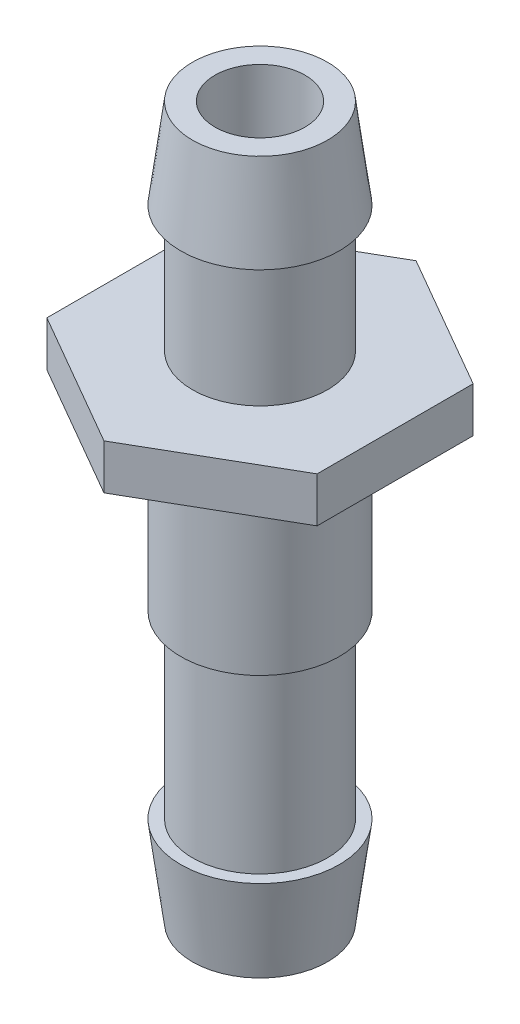
SolidWorks part; units mm, degrees
material "1060 Alloy"
ref_plane "Front Plane" through (0, 0, 0) normal (0, 0, 1) x (1, 0, 0)
ref_plane "Top Plane" through (0, 0, 0) normal (0, 1, 0) x (1, 0, 0)
ref_plane "Right Plane" through (0, 0, 0) normal (1, 0, 0) x (0, 0, -1)
sketch "Sketch1" plane through (0, 0, 0) normal (0, 1, 0) x (1, 0, 0)
  circle A0 centre (0, 0) radius 4.7625
  circle A1 centre (0, 0) radius 3.175
extrude "Extrude1" add sketch "Sketch1" along normal blind 15.24
sketch "Sketch2" plane through (0, 0, 0) normal (0, -1, 0) x (1, 0, 0)
  line L0 (0, 10.9985) -> (0, -10.9985) construction
  line L1 (9.525, 5.4993) -> (9.525, -5.4993)
  line L2 (0, 10.9985) -> (9.525, 5.4993)
  line L3 (0, -10.9985) -> (9.525, -5.4993)
  line L4 (0, -10.9985) -> (-9.525, -5.4993)
  line L5 (0, 10.9985) -> (-9.525, 5.4993)
  line L6 (-9.525, 5.4993) -> (-9.525, -5.4993)
  line L7 (0, 0) -> (0, -10.9985) construction
  line L8 (0, 0) -> (9.525, -5.4993) construction
  line L9 (0, 0) -> (9.525, 5.4993) construction
  circle A0 centre (0, 0) radius 3.175
  dimension "D1" = 19.05
extrude "Extrude2" add sketch "Sketch2" along normal blind 3.175
sketch "Sketch3" plane through (0, -3.175, 0) normal (0, -1, 0) x (1, 0, 0)
  circle A0 centre (0, 0) radius 3.175
  circle A1 centre (0, 0) radius 4.7625
extrude "Extrude3" add sketch "Sketch3" along normal blind 31.75
sketch "Sketch4" plane through (0, -3.175, 0) normal (0, -1, 0) x (1, 0, 0)
  circle A0 centre (0, 0) radius 5.588
  circle A1 centre (0, 0) radius 7.366
extrude "Cut-Extrude1" cut sketch "Sketch4" against normal blind 1.5875
sketch "Sketch5" plane through (0, 15.24, 0) normal (0, 1, 0) x (-1, 0, 0)
  circle A0 centre (0, 0) radius 4.7625
  circle A1 centre (0, 0) radius 5.588
extrude "Extrude4" add sketch "Sketch5" against normal blind 6.35
sketch "Sketch8" plane through (0, -34.925, 0) normal (0, -1, 0) x (1, 0, 0)
  circle A0 centre (0, 0) radius 4.7625
  circle A1 centre (0, 0) radius 5.588
extrude "Extrude5" add sketch "Sketch8" against normal blind 6.35
sketch "Sketch7" plane through (0, 0, 0) normal (1, 0, 0) x (0, 0, -1)
  line L0 (-5.588, 8.89) -> (-4.7625, 15.24)
  line L1 (5.588, 15.24) -> (-5.588, 15.24) construction
  line L2 (0, 15.24) -> (0, 0) construction
  line L3 (-4.7625, 15.24) -> (-5.588, 15.24)
  line L4 (-5.588, 15.24) -> (-5.588, 8.89)
  line L5 (9.525, -9.8425) -> (-9.525, -9.8425) construction
  line L6 (-5.588, -34.925) -> (-5.588, -28.575)
  line L7 (-4.7625, -34.925) -> (-5.588, -34.925)
  line L8 (-5.588, -28.575) -> (-4.7625, -34.925)
  dimension "D1" = 0.8255
revolve "Cut-Revolve1" cut sketch "Sketch7" angle 360 about L2
sketch "Sketch9" plane through (0, -3.175, 0) normal (0, -1, 0) x (1, 0, 0)
  circle A0 centre (0, 0) radius 4.7625
  circle A1 centre (0, 0) radius 5.588
extrude "Extrude6" add sketch "Sketch9" along normal blind 12.7
